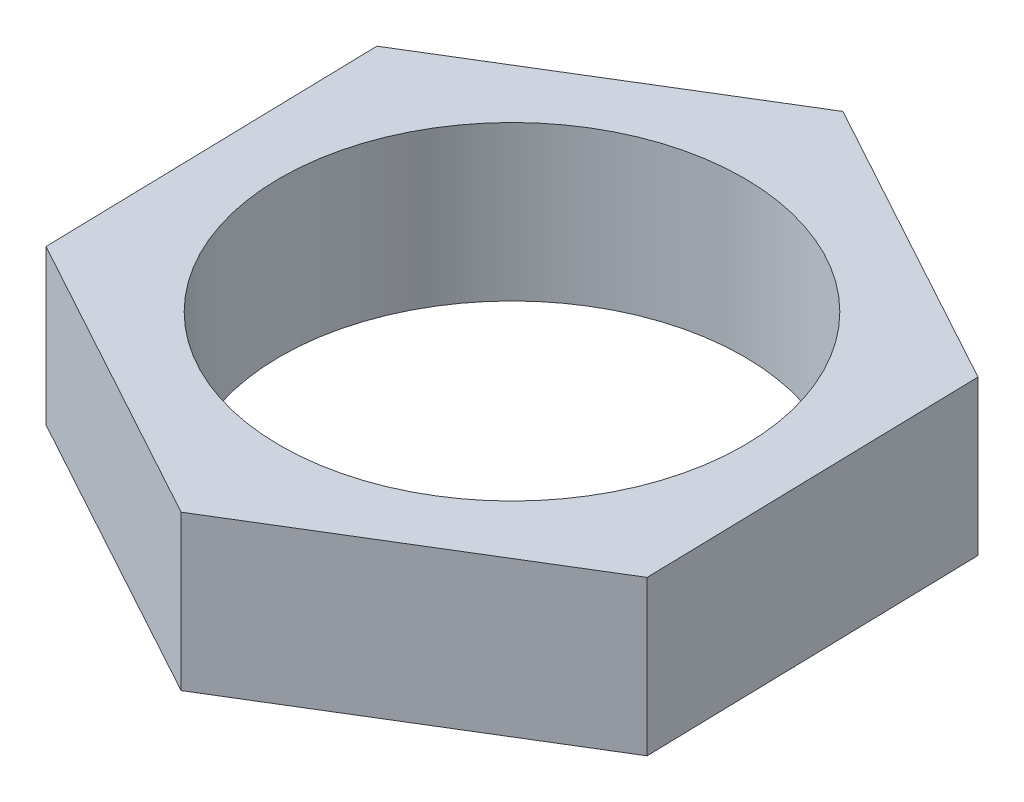
SolidWorks part; units mm, degrees
ref_plane "Front Plane" through (0, 0, 0) normal (0, 0, 1) x (1, 0, 0)
ref_plane "Top Plane" through (0, 0, 0) normal (0, 1, 0) x (1, 0, 0)
ref_plane "Right Plane" through (0, 0, 0) normal (1, 0, 0) x (0, 0, -1)
sketch "Sketch1" plane through (0, 0, 0) normal (0, 1, 0) x (1, 0, 0)
  line L1 (9.6281, -5.2567) -> (9.3665, 5.7098)
  line L2 (9.3665, 5.7098) -> (-0.2616, 10.9665)
  line L3 (-0.2616, 10.9665) -> (-9.6281, 5.2567)
  line L4 (-9.6281, 5.2567) -> (-9.3665, -5.7098)
  line L5 (-9.3665, -5.7098) -> (0.2616, -10.9665)
  line L6 (0.2616, -10.9665) -> (9.6281, -5.2567)
  circle A0 centre (0, 0) radius 9.5 construction
  circle A1 centre (0, 0) radius 9.5
  dimension "D1" = 19
extrude "Boss-Extrude1" add sketch "Sketch1" along normal blind 5 contours L3 L4 L5 L6 L1 L2
sketch "Sketch3" plane through (0, 5, 0) normal (0, 1, 0) x (1, 0, 0)
  circle A0 centre (0, 0) radius 7.5
extrude "Cut-Extrude1" cut sketch "Sketch3" against normal blind 5 contours A0
